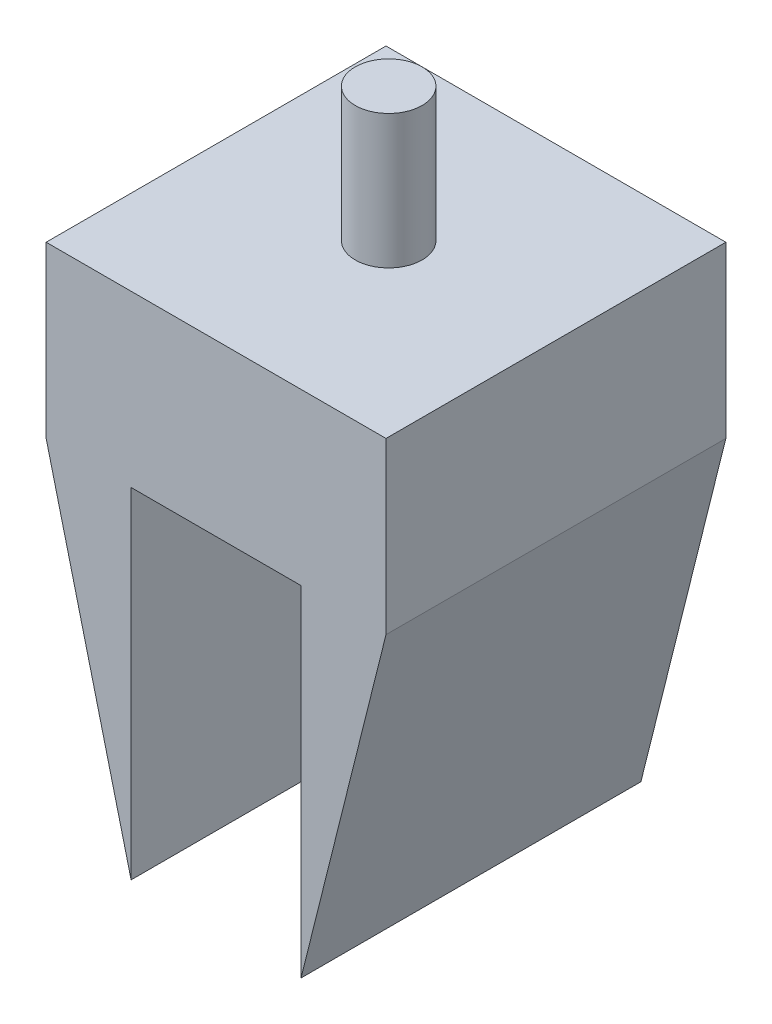
SolidWorks part; units mm, degrees
ref_plane "Front Plane" through (0, 0, 0) normal (0, 0, 1) x (1, 0, 0)
ref_plane "Top Plane" through (0, 0, 0) normal (0, 1, 0) x (1, 0, 0)
ref_plane "Right Plane" through (0, 0, 0) normal (1, 0, 0) x (0, 0, -1)
sketch "Sketch1" plane through (0, 0, 0) normal (0, 0, 1) x (1, 0, 0)
  line L0 (0, 0) -> (0, 76.2)
  line L1 (0, 76.2) -> (50.8, 76.2)
  line L2 (50.8, 76.2) -> (50.8, 0)
  line L3 (0, 0) -> (12.7, 0)
  line L4 (50.8, 0) -> (38.1, 0)
  line L5 (38.1, 0) -> (38.1, 50.8)
  line L6 (38.1, 50.8) -> (12.7, 50.8)
  line L7 (12.7, 50.8) -> (12.7, 0)
  dimension "D1" = 76.2
  dimension "D2" = 50.8
  dimension "D3" = 76.2
  dimension "D4" = 12.7
  dimension "D5" = 12.7
  dimension "D6" = 50.8
  dimension "D7" = 25.4
  dimension "D8" = 50.8
extrude "Boss-Extrude2" add sketch "Sketch1" against normal blind 50.8
sketch "Sketch3" plane through (0, 76.2, 0) normal (0, 1, 0) x (1, 0, 0)
  circle A0 centre (25.4, 25.8) radius 5
  dimension "D1" = 10
sketch "Sketch4" plane through (0, 0, 0) normal (0, 0, 1) x (1, 0, 0)
  line L0 (0, 50.8) -> (12.7, 0)
  line L1 (0, 76.2) -> (0, 0) construction
  line L2 (0, 50.8) -> (0, 0)
  line L3 (0, 0) -> (12.7, 0)
  dimension "D1" = 52.3634
  dimension "D2" = 50.8
  dimension "D3" = 12.7
extrude "Cut-Extrude2" cut sketch "Sketch4" against normal blind 63.5
sketch "Sketch5" plane through (0, 0, 0) normal (0, 0, 1) x (1, 0, 0)
  line L0 (50.8, 50.8) -> (38.1, 0)
  line L1 (50.8, 0) -> (50.8, 76.2) construction
  line L2 (38.1, 0) -> (50.8, 0)
  line L3 (50.8, 0) -> (50.8, 50.8)
  dimension "D1" = 52.3634
  dimension "D2" = 12.7
  dimension "D3" = 50.8
extrude "Cut-Extrude3" cut sketch "Sketch5" against normal blind 63.5
extrude "Boss-Extrude3" add sketch "Sketch3" along normal blind 20
